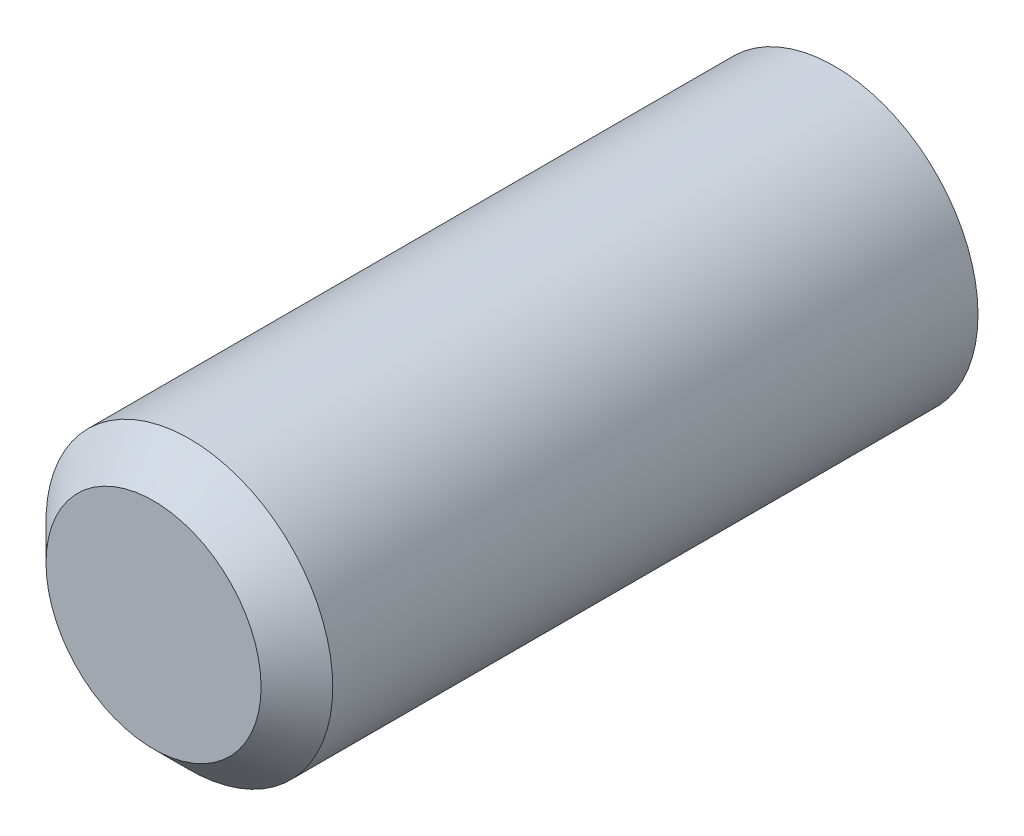
SolidWorks part; units mm, degrees
ref_plane "Front Plane" through (0, 0, 0) normal (0, 0, 1) x (1, 0, 0)
ref_plane "Top Plane" through (0, 0, 0) normal (0, 1, 0) x (1, 0, 0)
ref_plane "Right Plane" through (0, 0, 0) normal (1, 0, 0) x (0, 0, -1)
sketch "Sketch1" plane through (0, 0, 0) normal (0, 0, 1) x (1, 0, 0)
  circle A0 centre (0, 0) radius 10
  dimension "D1" = 20
extrude "Boss-Extrude1" add sketch "Sketch1" along normal blind 47.5
chamfer "Chamfer1" distance 2.5 angle 45 1 edges at (10, 0, 47.5)
sketch "Sketch3" plane through (0, 0, 47.5) normal (0, 0, 1) x (1, 0, 0)
  circle A0 centre (0, 0) radius 9.188
  dimension "D1" = 18.376
curve "Helix/Spiral1" pitch 2.5 height 47.5 turns 19
